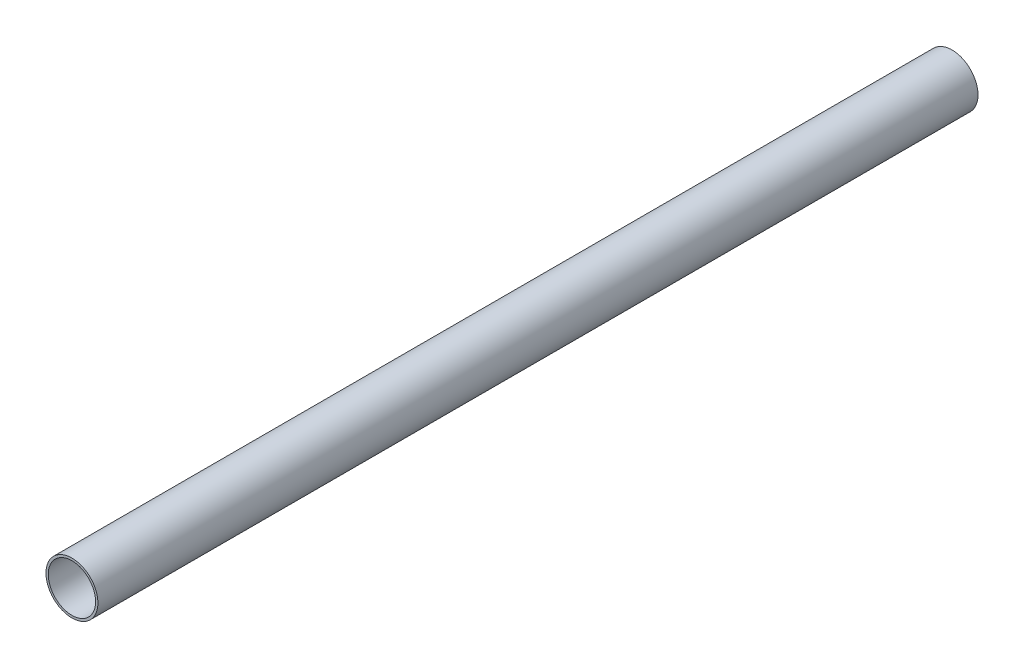
SolidWorks part; units mm, degrees
ref_plane "Front" through (0, 0, 0) normal (0, 0, 1) x (1, 0, 0)
ref_plane "Top" through (0, 0, 0) normal (0, 1, 0) x (1, 0, 0)
ref_plane "Side" through (0, 0, 0) normal (1, 0, 0) x (0, 0, -1)
sketch "PipeSketch" plane through (0, 0, 0) normal (0, 0, 1) x (1, 0, 0)
  circle A0 centre (0, 0) radius 161.925
  circle A1 centre (0, 0) radius 147.6502
  dimension "OuterDiameter" = 323.85
  dimension "InnerDiameter" = 295.3004
extrude "Extrusion" add sketch "PipeSketch" along normal blind 5486.4
sketch "FilterSketch" plane through (0, 0, 0) normal (0, 0, 1) x (1, 0, 0)
  circle A0 centre (0, 0) radius 152.4 construction
  dimension "NominalDiameter" = 304.8
